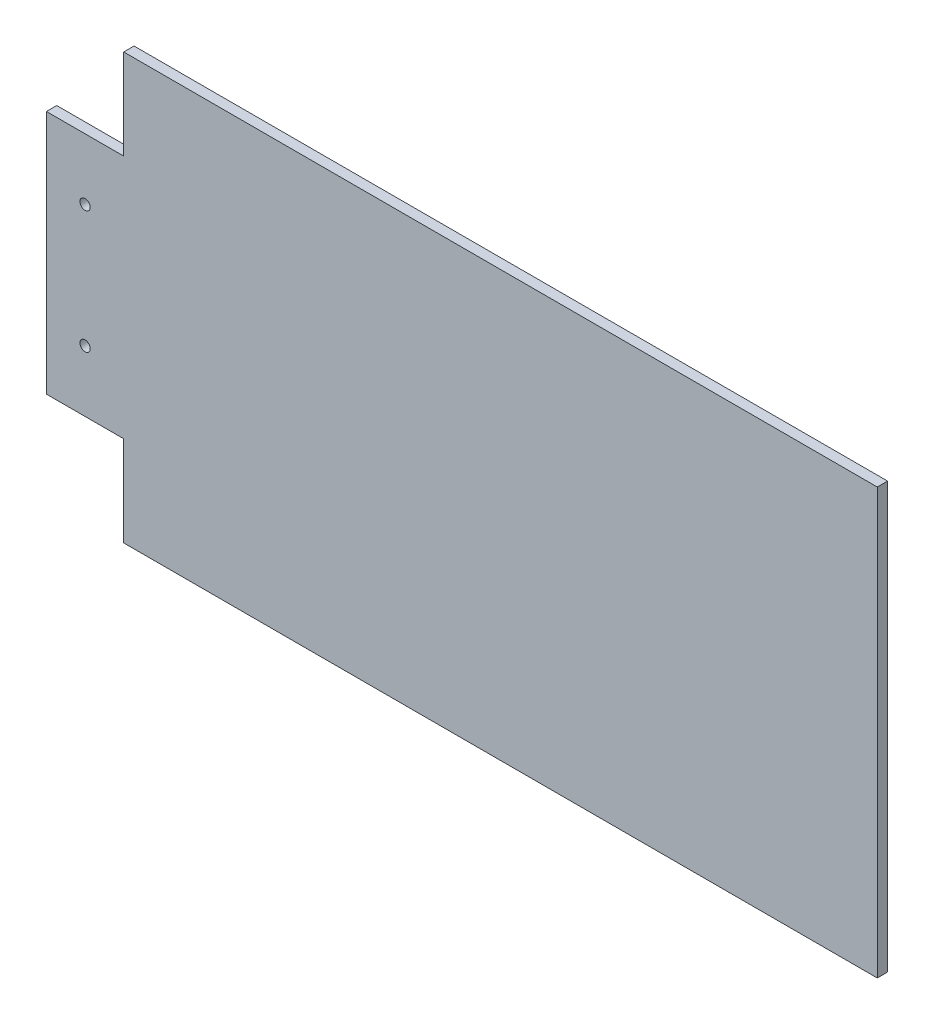
SolidWorks part; units mm, degrees
ref_plane "Front Plane" through (0, 0, 0) normal (0, 0, 1) x (1, 0, 0)
ref_plane "Top Plane" through (0, 0, 0) normal (0, 1, 0) x (1, 0, 0)
ref_plane "Right Plane" through (0, 0, 0) normal (1, 0, 0) x (0, 0, -1)
sketch "Sketch1" plane through (0, 0, 0) normal (0, 0, 1) x (1, 0, 0)
  line L0 (1290.3485, 1267.2212) -> (1320.3485, 1267.2212)
  line L1 (1320.3485, 1267.2212) -> (1320.3485, 1302.2212)
  line L2 (1320.3485, 1302.2212) -> (1612.7485, 1302.2212)
  line L3 (1612.7485, 1302.2212) -> (1612.7485, 1137.2212)
  line L4 (1612.7485, 1137.2212) -> (1320.3485, 1137.2212)
  line L7 (1290.3485, 1172.2212) -> (1290.3485, 1267.2212)
  line L12 (1290.3485, 1172.2212) -> (1320.3485, 1172.2212)
  line L17 (1320.3485, 1172.2212) -> (1320.3485, 1137.2212)
  circle A8 centre (1305.3485, 1243.4712) radius 2
  circle A11 centre (1305.3485, 1195.9712) radius 2
  point P30 (1612.7485, 1219.7212)
extrude "Boss-Extrude1" add sketch "Sketch1" along normal blind 4
